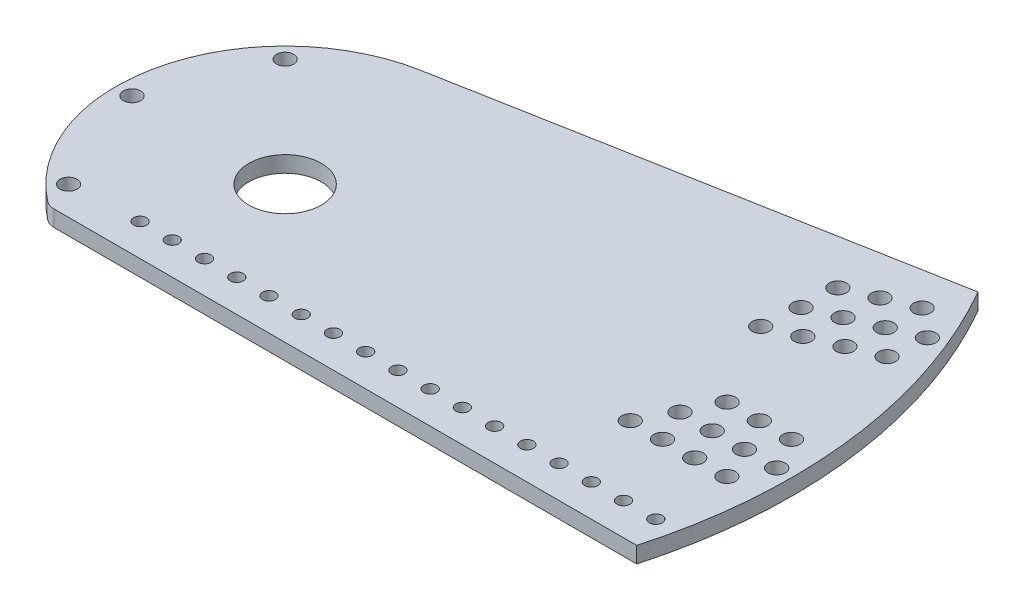
SolidWorks part; units mm, degrees
ref_plane "Front Plane" through (0, 0, 0) normal (0, 0, 1) x (1, 0, 0)
ref_plane "Top Plane" through (0, 0, 0) normal (0, 1, 0) x (1, 0, 0)
ref_plane "Right Plane" through (0, 0, 0) normal (1, 0, 0) x (0, 0, -1)
ref_plane "Plane1" through (0, 0, 0) normal (0, -1, 0) x (1, 0, 0)
sketch "Sketch1" plane through (0, 0, 0) normal (0, -1, 0) x (1, 0, 0)
  line L0 (231.775, 53.975) -> (-37.0265, 53.975)
  line L1 (-25.4, -65.7616) -> (-25.4, -230.9908)
  line L2 (238.125, 0) -> (238.125, 47.625)
  circle A0 centre (-60.325, 0) radius 3.3782
  circle A1 centre (-42.6562, 42.6562) radius 3.3782
  circle A2 centre (-42.6562, -42.6562) radius 3.3782
  circle A3 centre (0, -155.575) radius 3.3782
  circle A4 centre (0, -168.275) radius 3.3782
  circle A5 centre (0, -180.975) radius 3.3782
  circle A6 centre (0, -193.675) radius 3.3782
  circle A7 centre (0, -206.375) radius 3.3782
  circle A8 centre (0, -219.075) radius 3.3782
  circle A9 centre (59.536, -143.7326) radius 3.3782
  circle A10 centre (64.3961, -155.4658) radius 3.3782
  circle A11 centre (69.2561, -167.1991) radius 3.3782
  circle A12 centre (74.1162, -178.9324) radius 3.3782
  circle A13 centre (78.9763, -190.6656) radius 3.3782
  circle A14 centre (83.8364, -202.3989) radius 3.3782
  circle A15 centre (110.0081, -110.0081) radius 3.3782
  circle A16 centre (118.9884, -118.9884) radius 3.3782
  circle A17 centre (127.9686, -127.9686) radius 3.3782
  circle A18 centre (136.9489, -136.9489) radius 3.3782
  circle A19 centre (145.9292, -145.9292) radius 3.3782
  circle A20 centre (154.9094, -154.9094) radius 3.3782
  circle A21 centre (143.7326, -59.536) radius 3.3782
  circle A22 centre (155.4658, -64.3961) radius 3.3782
  circle A23 centre (167.1991, -69.2561) radius 3.3782
  circle A24 centre (178.9324, -74.1162) radius 3.3782
  circle A25 centre (190.6656, -78.9763) radius 3.3782
  circle A26 centre (202.3989, -83.8364) radius 3.3782
  circle A27 centre (155.575, 0) radius 3.3782
  circle A28 centre (168.275, 0) radius 3.3782
  circle A29 centre (180.975, 0) radius 3.3782
  circle A30 centre (193.675, 0) radius 3.3782
  circle A31 centre (206.375, 0) radius 3.3782
  circle A32 centre (219.075, 0) radius 3.3782
  circle A33 centre (0, 0) radius 14.2812
  circle A34 centre (148.6836, 12.7) radius 3.3782
  circle A35 centre (141.0863, -159.0468) radius 3.3782
  circle A36 centre (150.0365, -132.0759) radius 3.3782
  circle A37 centre (150.0666, -168.0271) radius 3.3782
  circle A38 centre (159.0167, -141.0562) radius 3.3782
  circle A39 centre (-12.7, -186.8262) radius 3.3782
  circle A40 centre (12.7, -174.0836) radius 3.3782
  circle A41 centre (-12.7, -199.5262) radius 3.3782
  circle A42 centre (12.7, -186.7836) radius 3.3782
  circle A43 centre (-12.7, -212.2262) radius 3.3782
  circle A44 centre (12.7, -199.4836) radius 3.3782
  circle A45 centre (-12.7, -224.9262) radius 3.3782
  circle A46 centre (12.7, -212.1836) radius 3.3782
  circle A47 centre (69.4822, -200.9315) radius 3.3782
  circle A48 centre (88.0723, -179.4387) radius 3.3782
  circle A49 centre (74.3423, -212.6648) radius 3.3782
  circle A50 centre (92.9324, -191.172) radius 3.3782
  circle A51 centre (50.0419, -153.9984) radius 3.3782
  circle A52 centre (68.632, -132.5056) radius 3.3782
  circle A53 centre (54.9019, -165.7317) radius 3.3782
  circle A54 centre (73.4921, -144.2389) radius 3.3782
  circle A55 centre (59.762, -177.465) radius 3.3782
  circle A56 centre (78.3522, -155.9722) radius 3.3782
  circle A57 centre (64.6221, -189.1982) radius 3.3782
  circle A58 centre (83.2123, -167.7055) radius 3.3782
  circle A59 centre (123.1258, -141.0863) radius 3.3782
  circle A60 centre (132.0759, -114.1154) radius 3.3782
  circle A61 centre (132.1061, -150.0666) radius 3.3782
  circle A62 centre (141.0562, -123.0957) radius 3.3782
  circle A63 centre (200.8922, -69.4659) radius 3.3782
  circle A64 centre (202.9446, -97.8088) radius 3.3782
  circle A65 centre (189.1589, -64.6058) radius 3.3782
  circle A66 centre (191.2114, -92.9487) radius 3.3782
  circle A67 centre (105.1653, -123.1258) radius 3.3782
  circle A68 centre (114.1154, -96.1549) radius 3.3782
  circle A69 centre (114.1456, -132.1061) radius 3.3782
  circle A70 centre (123.0957, -105.1352) radius 3.3782
  circle A71 centre (153.9591, -50.0256) radius 3.3782
  circle A72 centre (156.0115, -78.3685) radius 3.3782
  circle A73 centre (142.2258, -45.1655) radius 3.3782
  circle A74 centre (144.2783, -73.5084) radius 3.3782
  circle A75 centre (177.4256, -59.7457) radius 3.3782
  circle A76 centre (179.4781, -88.0886) radius 3.3782
  circle A77 centre (165.6923, -54.8856) radius 3.3782
  circle A78 centre (167.7448, -83.2286) radius 3.3782
  circle A79 centre (-12.7, -161.4262) radius 3.3782
  circle A80 centre (12.7, -148.6836) radius 3.3782
  circle A81 centre (-12.7, -174.1262) radius 3.3782
  circle A82 centre (12.7, -161.3836) radius 3.3782
  circle A83 centre (186.8262, -12.7) radius 3.3782
  circle A84 centre (174.0836, 12.7) radius 3.3782
  circle A85 centre (199.5262, -12.7) radius 3.3782
  circle A86 centre (186.7836, 12.7) radius 3.3782
  circle A87 centre (212.2262, -12.7) radius 3.3782
  circle A88 centre (199.4836, 12.7) radius 3.3782
  circle A89 centre (224.9262, -12.7) radius 3.3782
  circle A90 centre (212.1836, 12.7) radius 3.3782
  circle A91 centre (161.4262, -12.7) radius 3.3782
  circle A92 centre (174.1262, -12.7) radius 3.3782
  circle A93 centre (161.3836, 12.7) radius 3.3782
  circle A94 centre (225.425, 41.275) radius 2.5527
  circle A95 centre (212.725, 41.275) radius 2.5527
  circle A96 centre (200.025, 41.275) radius 2.5527
  circle A97 centre (187.325, 41.275) radius 2.5527
  circle A98 centre (174.625, 41.275) radius 2.5527
  circle A99 centre (161.925, 41.275) radius 2.5527
  circle A100 centre (149.225, 41.275) radius 2.5527
  circle A101 centre (136.525, 41.275) radius 2.5527
  circle A102 centre (123.825, 41.275) radius 2.5527
  circle A103 centre (111.125, 41.275) radius 2.5527
  circle A104 centre (98.425, 41.275) radius 2.5527
  circle A105 centre (73.025, 41.275) radius 2.5527
  circle A106 centre (85.725, 41.275) radius 2.5527
  circle A107 centre (60.325, 41.275) radius 2.5527
  circle A108 centre (47.625, 41.275) radius 2.5527
  circle A109 centre (34.925, 41.275) radius 2.5527
  circle A110 centre (22.225, 41.275) radius 2.5527
  circle A111 centre (9.525, 41.275) radius 2.5527
  circle A112 centre (-3.175, 41.275) radius 2.5527
  circle A113 centre (-15.875, 41.275) radius 2.5527
  circle A114 centre (-17.9605, 17.9605) radius 2.5527
  circle A115 centre (-17.9605, -17.9605) radius 2.5527
  circle A116 centre (17.9605, -17.9605) radius 2.5527
  circle A117 centre (17.9605, 17.9605) radius 2.5527
  circle A118 centre (52.1146, -6.35) radius 9.5885
  circle A119 centre (70.0751, 11.6105) radius 2.5527
  circle A120 centre (-17.9605, -34.5395) radius 2.5527
  circle A121 centre (17.9605, -70.4605) radius 2.5527
  circle A122 centre (70.0751, -24.3105) radius 2.5527
  circle A123 centre (34.154, -24.3105) radius 2.5527
  circle A124 centre (34.154, 11.6105) radius 2.5527
  circle A125 centre (0, -52.5) radius 19.177
  circle A126 centre (-17.9605, -70.4605) radius 4.1275
  circle A127 centre (17.9605, -34.5395) radius 4.1275
  arc A128 (-37.0265, 53.975) -> (-40.9241, 52.6382) centre (-37.0265, 47.625) ccw
  arc A129 (-40.9241, 52.6382) -> (-28.9891, -60.0432) centre (0, 0) ccw
  arc A130 (-28.9891, -60.0432) -> (-25.4, -65.7616) centre (-31.75, -65.7616) cw
  arc A131 (-25.4, -230.9908) -> (-19.5719, -237.3193) centre (-19.05, -230.9908) ccw
  arc A132 (-19.5719, -237.3193) -> (238.125, 0) centre (0, 0) ccw
  arc A133 (238.125, 47.625) -> (231.775, 53.975) centre (231.775, 47.625) ccw
extrude "Boss-Extrude1" add sketch "Sketch1" against normal blind 6.35
sketch "Sketch2" plane through (0, 6.35, 0) normal (0, 1, 0) x (1, 0, 0)
  circle A0 centre (0, 52.5) radius 19.177
  circle A1 centre (17.9605, 70.4605) radius 2.5527
  circle A2 centre (17.9605, 34.5395) radius 4.1275
  circle A3 centre (-17.9605, 34.5395) radius 2.5527
  circle A4 centre (-17.9605, 70.4605) radius 4.1275
  circle A5 centre (34.154, -11.6105) radius 2.5527
  circle A6 centre (52.1146, 6.35) radius 9.5885
  circle A7 centre (34.154, 24.3105) radius 2.5527
  circle A8 centre (70.0751, 24.3105) radius 2.5527
  circle A9 centre (70.0751, -11.6105) radius 2.5527
  circle A10 centre (17.9605, -17.9605) radius 2.5527
  circle A11 centre (-17.9605, -17.9605) radius 2.5527
  circle A12 centre (-17.9605, 17.9605) radius 2.5527
  circle A13 centre (17.9605, 17.9605) radius 2.5527
extrude "Boss-Extrude2" add sketch "Sketch2" against normal through all contours A4 | A3 | A12 | A11 | A10 | A9 | A6 | A2 | A0 | A8 | A7 | A5 | A1 | A13
sketch "Sketch3" plane through (0, 6.35, 0) normal (0, 1, 0) x (1, 0, 0)
  line L0 (0, 0) -> (167.7448, 83.2286) construction
  line L1 (0, 0) -> (123.1258, 141.0863) construction
  line L2 (186.8262, 12.7) -> (186.8262, -53.975) construction
  line L3 (231.775, -53.975) -> (-37.0265, -53.975) construction
  line L4 (0, 0) -> (186.8262, 12.7) construction
  line L6 (-28.9891, 60.0432) -> (-28.9891, 240.2011)
  line L7 (-28.9891, 240.2011) -> (143.8883, 240.2011)
  line L9 (92.9324, 191.172) -> (159.0167, 141.0562) construction
  line L12 (143.8883, 195.6216) -> (143.8883, 240.2011)
  line L14 (190.335, -61.1929) -> (235.0044, -61.1929)
  line L15 (241.8769, -21.6157) -> (241.8769, -61.1929)
  line L16 (241.8769, -61.1929) -> (235.0044, -61.1929)
  line L17 (173.283, 99.7245) -> (-12.0815, 65.5713)
  line L18 (145.5713, 94.6187) -> (182.0476, 82.6479) construction
  circle A0 centre (0, 0) radius 50.8 construction
  arc A3 (-12.0815, 65.5713) -> (-28.9891, 60.0432) centre (0, 0) ccw
  arc A4 (66.5215, 4.522) -> (43.8403, 50.2353) centre (0, 0) ccw construction
  arc A5 (190.335, -61.1929) -> (173.283, 99.7245) centre (0, 0) ccw
  arc A6 (241.8769, -21.6157) -> (143.8883, 195.6216) centre (0, 0) ccw
  dimension "D1" = 101.6
  dimension "D2" = 187.2574
extrude "Cut-Extrude1" cut sketch "Sketch3" against normal through all
sketch "Sketch4" plane through (0, 6.35, 0) normal (0, 1, 0) x (1, 0, 0)
  arc A2 (199.2831, 16.0694) -> (199.7123, 9.3269) centre (199.5262, 12.7) ccw
  arc A3 (188.0802, 67.8072) -> (190.264, 61.4135) centre (189.1589, 64.6058) ccw
  arc A4 (177.9641, 91.1086) -> (180.9408, 85.0435) centre (179.4781, 88.0886) ccw
  arc A7 (199.2831, 16.0694) -> (199.7123, 9.3269) centre (0, 0) cw
  arc A8 (177.9641, 91.1086) -> (180.9408, 85.0435) centre (0, 0) cw
  arc A10 (188.0802, 67.8072) -> (190.264, 61.4135) centre (0, 0) cw
  arc A11 (199.7122, -9.3295) -> (199.2829, -16.0722) centre (199.4836, -12.7) ccw
  arc A12 (199.2829, -16.0722) -> (199.7122, -9.3295) centre (0, 0) ccw
  arc A13 (199.7123, 9.3269) -> (190.264, 61.4135) centre (0, 0) ccw
extrude "Boss-Extrude3" add sketch "Sketch4" against normal up to surface (6.35 mm away) up to face at (-60.325, 0, 3.3782)
